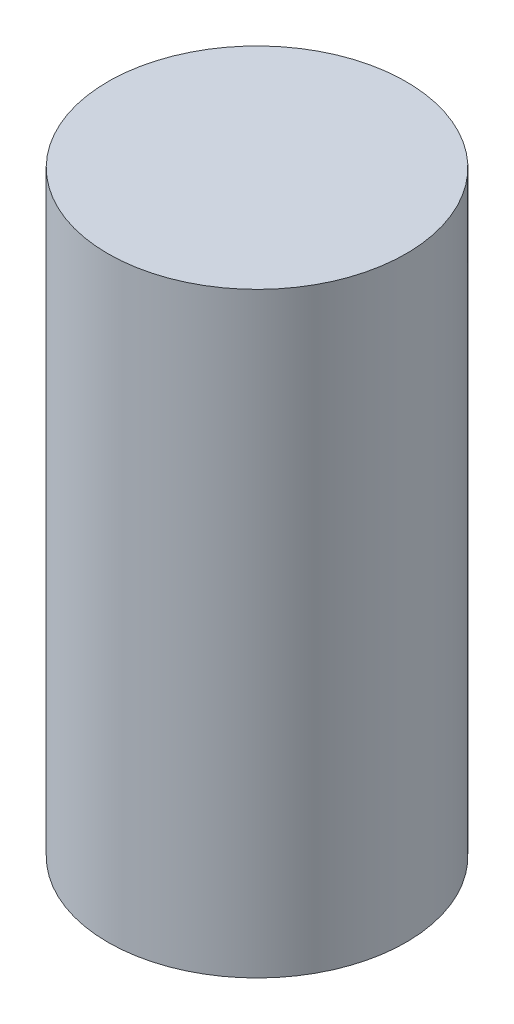
SolidWorks part; units mm, degrees
ref_plane "Front Plane" through (0, 0, 0) normal (0, 0, 1) x (1, 0, 0)
ref_plane "Top Plane" through (0, 0, 0) normal (0, 1, 0) x (1, 0, 0)
ref_plane "Right Plane" through (0, 0, 0) normal (1, 0, 0) x (0, 0, -1)
sketch "Sketch1" plane through (0, 0, 0) normal (0, 1, 0) x (1, 0, 0)
  circle A0 centre (0, 0) radius 10
  dimension "D1" = 20
extrude "Boss-Extrude1" add sketch "Sketch1" along normal blind 40
